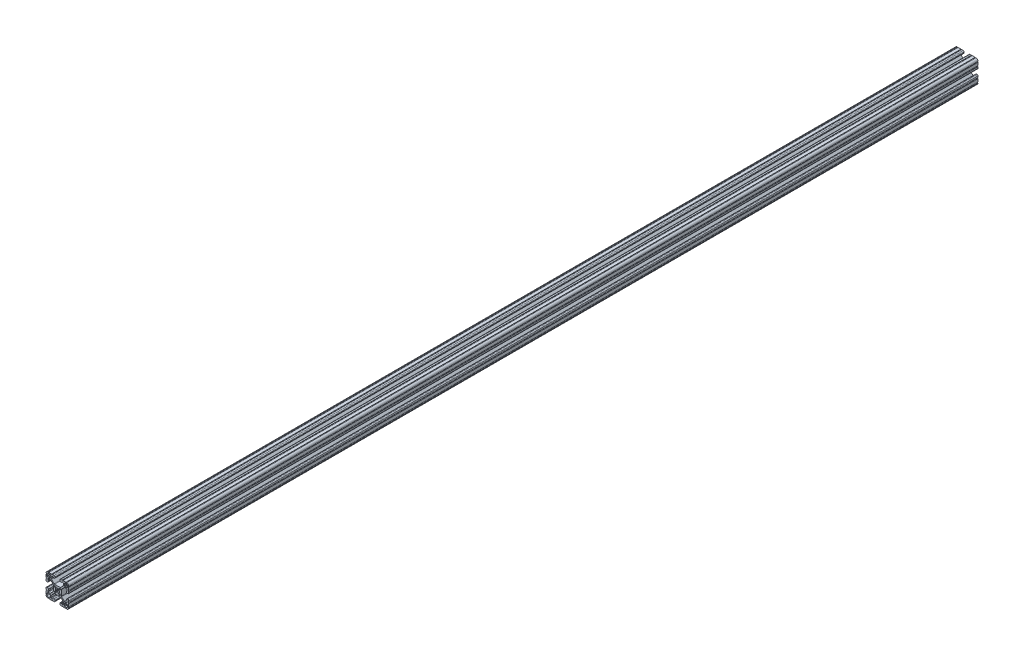
SolidWorks part; units mm, degrees
ref_plane "Front Plane" through (0, 0, 0) normal (0, 0, 1) x (1, 0, 0)
ref_plane "Top Plane" through (0, 0, 0) normal (0, 1, 0) x (1, 0, 0)
ref_plane "Right Plane" through (0, 0, 0) normal (1, 0, 0) x (0, 0, -1)
sketch "Sketch1" plane through (0, 0, 0) normal (0, 0, 1) x (1, 0, 0)
  line L0 (1.5823, 3.1988) -> (3.2921, 4.9085)
  line L1 (3.9207, 5.1689) -> (4.9149, 5.1689)
  line L2 (5.1689, 4.9149) -> (5.1689, 3.9207)
  line L3 (4.9085, 3.2921) -> (3.1988, 1.5823)
  line L4 (3.1988, -1.5823) -> (4.9085, -3.2921)
  line L5 (5.1689, -3.9207) -> (5.1689, -4.9149)
  line L6 (4.9149, -5.1689) -> (3.9207, -5.1689)
  line L7 (3.2921, -4.9085) -> (1.5823, -3.1988)
  line L8 (-1.5823, -3.1988) -> (-3.2921, -4.9085)
  line L9 (-3.9207, -5.1689) -> (-4.9149, -5.1689)
  line L10 (-5.1689, -4.9149) -> (-5.1689, -3.9207)
  line L11 (-4.9085, -3.2921) -> (-3.1988, -1.5823)
  line L12 (-3.1988, 1.5823) -> (-4.9085, 3.2921)
  line L13 (-5.1689, 3.9207) -> (-5.1689, 4.9149)
  line L14 (-4.9149, 5.1689) -> (-3.9207, 5.1689)
  line L15 (-3.2921, 4.9085) -> (-1.5823, 3.1988)
  line L16 (-11.8669, 14.0194) -> (-11.8669, 12.2479)
  line L17 (-12.2479, 11.8669) -> (-14.0195, 11.8669)
  line L18 (-14.0213, 11.8676) -> (-14.5575, 12.4039)
  line L19 (-14.5611, 12.4039) -> (-15.0973, 11.8676)
  line L20 (-15.0991, 11.8669) -> (-16.8707, 11.8669)
  line L21 (-17.2517, 12.2479) -> (-17.2517, 14.4577)
  line L22 (-14.4577, 17.2517) -> (-12.2479, 17.2517)
  line L23 (-11.8669, 16.8707) -> (-11.8669, 15.0991)
  line L24 (-11.8676, 15.0973) -> (-12.4039, 14.5611)
  line L25 (-12.4039, 14.5575) -> (-11.8676, 14.0212)
  line L26 (-14.0194, -11.8669) -> (-12.2479, -11.8669)
  line L27 (-11.8669, -12.2479) -> (-11.8669, -14.0195)
  line L28 (-11.8676, -14.0213) -> (-12.4039, -14.5575)
  line L29 (-12.4039, -14.5611) -> (-11.8676, -15.0973)
  line L30 (-11.8669, -15.0991) -> (-11.8669, -16.8707)
  line L31 (-12.2479, -17.2517) -> (-14.4577, -17.2517)
  line L32 (-17.2517, -14.4577) -> (-17.2517, -12.2479)
  line L33 (-16.8707, -11.8669) -> (-15.0991, -11.8669)
  line L34 (-15.0973, -11.8676) -> (-14.5611, -12.4039)
  line L35 (-14.5575, -12.4039) -> (-14.0212, -11.8676)
  line L36 (11.8669, -14.0194) -> (11.8669, -12.2479)
  line L37 (12.2479, -11.8669) -> (14.0195, -11.8669)
  line L38 (14.0213, -11.8676) -> (14.5575, -12.4039)
  line L39 (14.5611, -12.4039) -> (15.0973, -11.8676)
  line L40 (15.0991, -11.8669) -> (16.8707, -11.8669)
  line L41 (17.2517, -12.2479) -> (17.2517, -14.4577)
  line L42 (14.4577, -17.2517) -> (12.2479, -17.2517)
  line L43 (11.8669, -16.8707) -> (11.8669, -15.0991)
  line L44 (11.8676, -15.0973) -> (12.4039, -14.5611)
  line L45 (12.4039, -14.5575) -> (11.8676, -14.0212)
  line L46 (14.0194, 11.8669) -> (12.2479, 11.8669)
  line L47 (11.8669, 12.2479) -> (11.8669, 14.0195)
  line L48 (11.8676, 14.0213) -> (12.4039, 14.5575)
  line L49 (12.4039, 14.5611) -> (11.8676, 15.0973)
  line L50 (11.8669, 15.0991) -> (11.8669, 16.8707)
  line L51 (12.2479, 17.2517) -> (14.4577, 17.2517)
  line L52 (17.2517, 14.4577) -> (17.2517, 12.2479)
  line L53 (16.8707, 11.8669) -> (15.0991, 11.8669)
  line L54 (15.0973, 11.8676) -> (14.5611, 12.4039)
  line L55 (14.5575, 12.4039) -> (14.0212, 11.8676)
  line L56 (6.3498, -14.9848) -> (5.6531, -14.9848)
  line L57 (4.0778, -16.5601) -> (4.0778, -17.4747)
  line L58 (5.6531, -19.05) -> (7.9756, -19.05)
  line L59 (9.4996, -19.05) -> (14.2981, -19.05)
  line L60 (19.05, -14.3256) -> (19.05, -9.4996)
  line L61 (19.05, -7.9756) -> (19.05, -5.6531)
  line L62 (17.4747, -4.0778) -> (16.5601, -4.0778)
  line L63 (14.9848, -5.6531) -> (14.9848, -6.3498)
  line L64 (15.3661, -6.731) -> (15.6969, -6.731)
  line L65 (16.0782, -7.1122) -> (16.0782, -9.3968)
  line L66 (15.1881, -10.287) -> (12.3526, -10.2871)
  line L67 (11.4535, -9.9142) -> (7.1147, -5.5659)
  line L68 (6.7437, -4.6689) -> (6.7437, 4.6414)
  line L69 (7.1147, 5.5384) -> (11.481, 9.9142)
  line L70 (12.38, 10.2871) -> (15.1881, 10.287)
  line L71 (16.0782, 9.3968) -> (16.0782, 7.1122)
  line L72 (15.6969, 6.731) -> (15.3661, 6.731)
  line L73 (14.9848, 6.3498) -> (14.9848, 5.6531)
  line L74 (16.5601, 4.0778) -> (17.4747, 4.0778)
  line L75 (19.05, 5.6531) -> (19.05, 7.9756)
  line L76 (19.05, 9.4996) -> (19.05, 14.2981)
  line L77 (14.3256, 19.05) -> (9.4996, 19.05)
  line L78 (7.9756, 19.05) -> (5.6531, 19.05)
  line L79 (4.0778, 17.4747) -> (4.0778, 16.5601)
  line L80 (5.6531, 14.9848) -> (6.3498, 14.9848)
  line L81 (6.731, 15.3661) -> (6.731, 15.6969)
  line L82 (7.1122, 16.0782) -> (9.3968, 16.0782)
  line L83 (10.287, 15.1881) -> (10.2871, 12.3526)
  line L84 (9.9142, 11.4535) -> (5.5659, 7.1147)
  line L85 (4.6689, 6.7437) -> (-4.6414, 6.7437)
  line L86 (-5.5384, 7.1147) -> (-9.9142, 11.481)
  line L87 (-10.2871, 12.38) -> (-10.287, 15.1881)
  line L88 (-9.3968, 16.0782) -> (-7.1122, 16.0782)
  line L89 (-6.731, 15.6969) -> (-6.731, 15.3661)
  line L90 (-6.3498, 14.9848) -> (-5.6531, 14.9848)
  line L91 (-4.0778, 16.5601) -> (-4.0778, 17.4747)
  line L92 (-5.6531, 19.05) -> (-7.9756, 19.05)
  line L93 (-9.4996, 19.05) -> (-14.2981, 19.05)
  line L94 (-19.05, 14.3256) -> (-19.05, 9.4996)
  line L95 (-19.05, 7.9756) -> (-19.05, 5.6531)
  line L96 (-17.4747, 4.0778) -> (-16.5601, 4.0778)
  line L97 (-14.9848, 5.6531) -> (-14.9848, 6.3498)
  line L98 (-15.3661, 6.731) -> (-15.6969, 6.731)
  line L99 (-16.0782, 7.1122) -> (-16.0782, 9.3968)
  line L100 (-15.1881, 10.287) -> (-12.3526, 10.2871)
  line L101 (-11.4535, 9.9142) -> (-7.1147, 5.5659)
  line L102 (-6.7437, 4.6689) -> (-6.7437, -4.6414)
  line L103 (-7.1147, -5.5384) -> (-11.481, -9.9142)
  line L104 (-12.38, -10.2871) -> (-15.1881, -10.287)
  line L105 (-16.0782, -9.3968) -> (-16.0782, -7.1122)
  line L106 (-15.6969, -6.731) -> (-15.3661, -6.731)
  line L107 (-14.9848, -6.3498) -> (-14.9848, -5.6531)
  line L108 (-16.5601, -4.0778) -> (-17.4747, -4.0778)
  line L109 (-19.05, -5.6531) -> (-19.05, -7.9756)
  line L110 (-19.05, -9.4996) -> (-19.05, -14.2981)
  line L111 (-14.3256, -19.05) -> (-9.4996, -19.05)
  line L112 (-7.9756, -19.05) -> (-5.6531, -19.05)
  line L113 (-4.0778, -17.4747) -> (-4.0778, -16.5601)
  line L114 (-5.6531, -14.9848) -> (-6.3498, -14.9848)
  line L115 (-6.731, -15.3661) -> (-6.731, -15.6969)
  line L116 (-7.1122, -16.0782) -> (-9.3968, -16.0782)
  line L117 (-10.287, -15.1881) -> (-10.2871, -12.3526)
  line L118 (-9.9142, -11.4535) -> (-5.5659, -7.1147)
  line L119 (-4.6689, -6.7437) -> (4.6414, -6.7437)
  line L120 (5.5384, -7.1147) -> (9.9142, -11.481)
  line L121 (10.2871, -12.38) -> (10.287, -15.1881)
  line L122 (9.3968, -16.0782) -> (7.1122, -16.0782)
  line L123 (6.731, -15.6969) -> (6.731, -15.3661)
  arc A0 (1.178, 3.1119) -> (1.5823, 3.1988) centre (1.3129, 3.4682) ccw
  arc A1 (3.9207, 5.1689) -> (3.2921, 4.9085) centre (3.9207, 4.2799) ccw
  arc A2 (5.1689, 4.9149) -> (4.9149, 5.1689) centre (4.9149, 4.9149) ccw
  arc A3 (4.9085, 3.2921) -> (5.1689, 3.9207) centre (4.2799, 3.9207) ccw
  arc A4 (3.1988, 1.5823) -> (3.1119, 1.178) centre (3.4682, 1.3129) ccw
  arc A5 (3.1119, -1.178) -> (3.1119, 1.178) centre (0, 0) ccw
  arc A6 (3.1119, -1.178) -> (3.1988, -1.5823) centre (3.4682, -1.3129) ccw
  arc A7 (5.1689, -3.9207) -> (4.9085, -3.2921) centre (4.2799, -3.9207) ccw
  arc A8 (4.9149, -5.1689) -> (5.1689, -4.9149) centre (4.9149, -4.9149) ccw
  arc A9 (3.2921, -4.9085) -> (3.9207, -5.1689) centre (3.9207, -4.2799) ccw
  arc A10 (1.5823, -3.1988) -> (1.178, -3.1119) centre (1.3129, -3.4682) ccw
  arc A11 (-1.178, -3.1119) -> (1.178, -3.1119) centre (0, 0) ccw
  arc A12 (-1.178, -3.1119) -> (-1.5823, -3.1988) centre (-1.3129, -3.4682) ccw
  arc A13 (-3.9207, -5.1689) -> (-3.2921, -4.9085) centre (-3.9207, -4.2799) ccw
  arc A14 (-5.1689, -4.9149) -> (-4.9149, -5.1689) centre (-4.9149, -4.9149) ccw
  arc A15 (-4.9085, -3.2921) -> (-5.1689, -3.9207) centre (-4.2799, -3.9207) ccw
  arc A16 (-3.1988, -1.5823) -> (-3.1119, -1.178) centre (-3.4682, -1.3129) ccw
  arc A17 (-3.1119, 1.178) -> (-3.1119, -1.178) centre (0, 0) ccw
  arc A18 (-3.1119, 1.178) -> (-3.1988, 1.5823) centre (-3.4682, 1.3129) ccw
  arc A19 (-5.1689, 3.9207) -> (-4.9085, 3.2921) centre (-4.2799, 3.9207) ccw
  arc A20 (-4.9149, 5.1689) -> (-5.1689, 4.9149) centre (-4.9149, 4.9149) ccw
  arc A21 (-3.2921, 4.9085) -> (-3.9207, 5.1689) centre (-3.9207, 4.2799) ccw
  arc A22 (-1.5823, 3.1988) -> (-1.178, 3.1119) centre (-1.3129, 3.4682) ccw
  arc A23 (1.178, 3.1119) -> (-1.178, 3.1119) centre (0, 0) ccw
  arc A24 (-11.8669, 14.0194) -> (-11.8676, 14.0212) centre (-11.8694, 14.0194) ccw
  arc A25 (-12.2479, 11.8669) -> (-11.8669, 12.2479) centre (-12.2479, 12.2479) ccw
  arc A26 (-14.0213, 11.8676) -> (-14.0195, 11.8669) centre (-14.0195, 11.8694) ccw
  arc A27 (-14.5575, 12.4039) -> (-14.5611, 12.4039) centre (-14.5593, 12.4021) ccw
  arc A28 (-15.0991, 11.8669) -> (-15.0973, 11.8676) centre (-15.0991, 11.8694) ccw
  arc A29 (-17.2517, 12.2479) -> (-16.8707, 11.8669) centre (-16.8707, 12.2479) ccw
  arc A30 (-14.4577, 17.2517) -> (-17.2517, 14.4577) centre (-14.4577, 14.4577) ccw
  arc A31 (-11.8669, 16.8707) -> (-12.2479, 17.2517) centre (-12.2479, 16.8707) ccw
  arc A32 (-11.8676, 15.0973) -> (-11.8669, 15.0991) centre (-11.8694, 15.0991) ccw
  arc A33 (-12.4039, 14.5611) -> (-12.4039, 14.5575) centre (-12.4021, 14.5593) ccw
  arc A34 (-14.0194, -11.8669) -> (-14.0212, -11.8676) centre (-14.0194, -11.8694) ccw
  arc A35 (-11.8669, -12.2479) -> (-12.2479, -11.8669) centre (-12.2479, -12.2479) ccw
  arc A36 (-11.8676, -14.0213) -> (-11.8669, -14.0195) centre (-11.8694, -14.0195) ccw
  arc A37 (-12.4039, -14.5575) -> (-12.4039, -14.5611) centre (-12.4021, -14.5593) ccw
  arc A38 (-11.8669, -15.0991) -> (-11.8676, -15.0973) centre (-11.8694, -15.0991) ccw
  arc A39 (-12.2479, -17.2517) -> (-11.8669, -16.8707) centre (-12.2479, -16.8707) ccw
  arc A40 (-17.2517, -14.4577) -> (-14.4577, -17.2517) centre (-14.4577, -14.4577) ccw
  arc A41 (-16.8707, -11.8669) -> (-17.2517, -12.2479) centre (-16.8707, -12.2479) ccw
  arc A42 (-15.0973, -11.8676) -> (-15.0991, -11.8669) centre (-15.0991, -11.8694) ccw
  arc A43 (-14.5611, -12.4039) -> (-14.5575, -12.4039) centre (-14.5593, -12.4021) ccw
  arc A44 (11.8669, -14.0194) -> (11.8676, -14.0212) centre (11.8694, -14.0194) ccw
  arc A45 (12.2479, -11.8669) -> (11.8669, -12.2479) centre (12.2479, -12.2479) ccw
  arc A46 (14.0213, -11.8676) -> (14.0195, -11.8669) centre (14.0195, -11.8694) ccw
  arc A47 (14.5575, -12.4039) -> (14.5611, -12.4039) centre (14.5593, -12.4021) ccw
  arc A48 (15.0991, -11.8669) -> (15.0973, -11.8676) centre (15.0991, -11.8694) ccw
  arc A49 (17.2517, -12.2479) -> (16.8707, -11.8669) centre (16.8707, -12.2479) ccw
  arc A50 (14.4577, -17.2517) -> (17.2517, -14.4577) centre (14.4577, -14.4577) ccw
  arc A51 (11.8669, -16.8707) -> (12.2479, -17.2517) centre (12.2479, -16.8707) ccw
  arc A52 (11.8676, -15.0973) -> (11.8669, -15.0991) centre (11.8694, -15.0991) ccw
  arc A53 (12.4039, -14.5611) -> (12.4039, -14.5575) centre (12.4021, -14.5593) ccw
  arc A54 (14.0194, 11.8669) -> (14.0212, 11.8676) centre (14.0194, 11.8694) ccw
  arc A55 (11.8669, 12.2479) -> (12.2479, 11.8669) centre (12.2479, 12.2479) ccw
  arc A56 (11.8676, 14.0213) -> (11.8669, 14.0195) centre (11.8694, 14.0195) ccw
  arc A57 (12.4039, 14.5575) -> (12.4039, 14.5611) centre (12.4021, 14.5593) ccw
  arc A58 (11.8669, 15.0991) -> (11.8676, 15.0973) centre (11.8694, 15.0991) ccw
  arc A59 (12.2479, 17.2517) -> (11.8669, 16.8707) centre (12.2479, 16.8707) ccw
  arc A60 (17.2517, 14.4577) -> (14.4577, 17.2517) centre (14.4577, 14.4577) ccw
  arc A61 (16.8707, 11.8669) -> (17.2517, 12.2479) centre (16.8707, 12.2479) ccw
  arc A62 (15.0973, 11.8676) -> (15.0991, 11.8669) centre (15.0991, 11.8694) ccw
  arc A63 (14.5611, 12.4039) -> (14.5575, 12.4039) centre (14.5593, 12.4021) ccw
  arc A64 (6.731, -15.3661) -> (6.3498, -14.9848) centre (6.35, -15.3658) ccw
  arc A65 (5.6531, -14.9848) -> (4.0778, -16.5601) centre (5.6526, -16.5596) ccw
  arc A66 (4.0778, -17.4747) -> (5.6531, -19.05) centre (5.6526, -17.4752) ccw
  arc A67 (9.4996, -19.05) -> (7.9756, -19.05) centre (8.7376, -19.05) ccw
  arc A68 (15.8221, -19.0496) -> (14.2981, -19.05) centre (15.0601, -19.05) ccw
  arc A69 (15.8221, -19.0496) -> (19.0499, -15.8496) centre (15.875, -15.875) ccw
  arc A70 (19.05, -14.3256) -> (19.0499, -15.8496) centre (19.05, -15.0876) ccw
  arc A71 (19.05, -7.9756) -> (19.05, -9.4996) centre (19.05, -8.7376) ccw
  arc A72 (19.05, -5.6531) -> (17.4747, -4.0778) centre (17.4752, -5.6526) ccw
  arc A73 (16.5601, -4.0778) -> (14.9848, -5.6531) centre (16.5596, -5.6526) ccw
  arc A74 (14.9848, -6.3498) -> (15.3661, -6.731) centre (15.3658, -6.35) ccw
  arc A75 (16.0782, -7.1122) -> (15.6969, -6.731) centre (15.6972, -7.112) ccw
  arc A76 (15.1881, -10.287) -> (16.0782, -9.3968) centre (15.1892, -9.398) ccw
  arc A77 (11.4535, -9.9142) -> (12.3526, -10.2871) centre (12.3525, -9.0171) ccw
  arc A78 (6.7437, -4.6689) -> (7.1147, -5.5659) centre (8.0137, -4.6689) ccw
  arc A79 (7.1147, 5.5384) -> (6.7437, 4.6414) centre (8.0137, 4.6414) ccw
  arc A80 (12.38, 10.2871) -> (11.481, 9.9142) centre (12.38, 9.0171) ccw
  arc A81 (16.0782, 9.3968) -> (15.1881, 10.287) centre (15.1892, 9.398) ccw
  arc A82 (15.6969, 6.731) -> (16.0782, 7.1122) centre (15.6972, 7.112) ccw
  arc A83 (15.3661, 6.731) -> (14.9848, 6.3498) centre (15.3658, 6.35) ccw
  arc A84 (14.9848, 5.6531) -> (16.5601, 4.0778) centre (16.5596, 5.6526) ccw
  arc A85 (17.4747, 4.0778) -> (19.05, 5.6531) centre (17.4752, 5.6526) ccw
  arc A86 (19.05, 9.4996) -> (19.05, 7.9756) centre (19.05, 8.7376) ccw
  arc A87 (19.0496, 15.8221) -> (19.05, 14.2981) centre (19.05, 15.0601) ccw
  arc A88 (19.0496, 15.8221) -> (15.8496, 19.0499) centre (15.875, 15.875) ccw
  arc A89 (14.3256, 19.05) -> (15.8496, 19.0499) centre (15.0876, 19.05) ccw
  arc A90 (7.9756, 19.05) -> (9.4996, 19.05) centre (8.7376, 19.05) ccw
  arc A91 (5.6531, 19.05) -> (4.0778, 17.4747) centre (5.6526, 17.4752) ccw
  arc A92 (4.0778, 16.5601) -> (5.6531, 14.9848) centre (5.6526, 16.5596) ccw
  arc A93 (6.3498, 14.9848) -> (6.731, 15.3661) centre (6.35, 15.3658) ccw
  arc A94 (7.1122, 16.0782) -> (6.731, 15.6969) centre (7.112, 15.6972) ccw
  arc A95 (10.287, 15.1881) -> (9.3968, 16.0782) centre (9.398, 15.1892) ccw
  arc A96 (9.9142, 11.4535) -> (10.2871, 12.3526) centre (9.0171, 12.3525) ccw
  arc A97 (4.6689, 6.7437) -> (5.5659, 7.1147) centre (4.6689, 8.0137) ccw
  arc A98 (-5.5384, 7.1147) -> (-4.6414, 6.7437) centre (-4.6414, 8.0137) ccw
  arc A99 (-10.2871, 12.38) -> (-9.9142, 11.481) centre (-9.0171, 12.38) ccw
  arc A100 (-9.3968, 16.0782) -> (-10.287, 15.1881) centre (-9.398, 15.1892) ccw
  arc A101 (-6.731, 15.6969) -> (-7.1122, 16.0782) centre (-7.112, 15.6972) ccw
  arc A102 (-6.731, 15.3661) -> (-6.3498, 14.9848) centre (-6.35, 15.3658) ccw
  arc A103 (-5.6531, 14.9848) -> (-4.0778, 16.5601) centre (-5.6526, 16.5596) ccw
  arc A104 (-4.0778, 17.4747) -> (-5.6531, 19.05) centre (-5.6526, 17.4752) ccw
  arc A105 (-9.4996, 19.05) -> (-7.9756, 19.05) centre (-8.7376, 19.05) ccw
  arc A106 (-15.8221, 19.0496) -> (-14.2981, 19.05) centre (-15.0601, 19.05) ccw
  arc A107 (-15.8221, 19.0496) -> (-19.0499, 15.8496) centre (-15.875, 15.875) ccw
  arc A108 (-19.05, 14.3256) -> (-19.0499, 15.8496) centre (-19.05, 15.0876) ccw
  arc A109 (-19.05, 7.9756) -> (-19.05, 9.4996) centre (-19.05, 8.7376) ccw
  arc A110 (-19.05, 5.6531) -> (-17.4747, 4.0778) centre (-17.4752, 5.6526) ccw
  arc A111 (-16.5601, 4.0778) -> (-14.9848, 5.6531) centre (-16.5596, 5.6526) ccw
  arc A112 (-14.9848, 6.3498) -> (-15.3661, 6.731) centre (-15.3658, 6.35) ccw
  arc A113 (-16.0782, 7.1122) -> (-15.6969, 6.731) centre (-15.6972, 7.112) ccw
  arc A114 (-15.1881, 10.287) -> (-16.0782, 9.3968) centre (-15.1892, 9.398) ccw
  arc A115 (-11.4535, 9.9142) -> (-12.3526, 10.2871) centre (-12.3525, 9.0171) ccw
  arc A116 (-6.7437, 4.6689) -> (-7.1147, 5.5659) centre (-8.0137, 4.6689) ccw
  arc A117 (-7.1147, -5.5384) -> (-6.7437, -4.6414) centre (-8.0137, -4.6414) ccw
  arc A118 (-12.38, -10.2871) -> (-11.481, -9.9142) centre (-12.38, -9.0171) ccw
  arc A119 (-16.0782, -9.3968) -> (-15.1881, -10.287) centre (-15.1892, -9.398) ccw
  arc A120 (-15.6969, -6.731) -> (-16.0782, -7.1122) centre (-15.6972, -7.112) ccw
  arc A121 (-15.3661, -6.731) -> (-14.9848, -6.3498) centre (-15.3658, -6.35) ccw
  arc A122 (-14.9848, -5.6531) -> (-16.5601, -4.0778) centre (-16.5596, -5.6526) ccw
  arc A123 (-17.4747, -4.0778) -> (-19.05, -5.6531) centre (-17.4752, -5.6526) ccw
  arc A124 (-19.05, -9.4996) -> (-19.05, -7.9756) centre (-19.05, -8.7376) ccw
  arc A125 (-19.0496, -15.8221) -> (-19.05, -14.2981) centre (-19.05, -15.0601) ccw
  arc A126 (-19.0496, -15.8221) -> (-15.8496, -19.0499) centre (-15.875, -15.875) ccw
  arc A127 (-14.3256, -19.05) -> (-15.8496, -19.0499) centre (-15.0876, -19.05) ccw
  arc A128 (-7.9756, -19.05) -> (-9.4996, -19.05) centre (-8.7376, -19.05) ccw
  arc A129 (-5.6531, -19.05) -> (-4.0778, -17.4747) centre (-5.6526, -17.4752) ccw
  arc A130 (-4.0778, -16.5601) -> (-5.6531, -14.9848) centre (-5.6526, -16.5596) ccw
  arc A131 (-6.3498, -14.9848) -> (-6.731, -15.3661) centre (-6.35, -15.3658) ccw
  arc A132 (-7.1122, -16.0782) -> (-6.731, -15.6969) centre (-7.112, -15.6972) ccw
  arc A133 (-10.287, -15.1881) -> (-9.3968, -16.0782) centre (-9.398, -15.1892) ccw
  arc A134 (-9.9142, -11.4535) -> (-10.2871, -12.3526) centre (-9.0171, -12.3525) ccw
  arc A135 (-4.6689, -6.7437) -> (-5.5659, -7.1147) centre (-4.6689, -8.0137) ccw
  arc A136 (5.5384, -7.1147) -> (4.6414, -6.7437) centre (4.6414, -8.0137) ccw
  arc A137 (10.2871, -12.38) -> (9.9142, -11.481) centre (9.0171, -12.38) ccw
  arc A138 (9.3968, -16.0782) -> (10.287, -15.1881) centre (9.398, -15.1892) ccw
  arc A139 (6.731, -15.6969) -> (7.1122, -16.0782) centre (7.112, -15.6972) ccw
extrude "Extrude1" add sketch "Sketch1" against normal blind 1524
